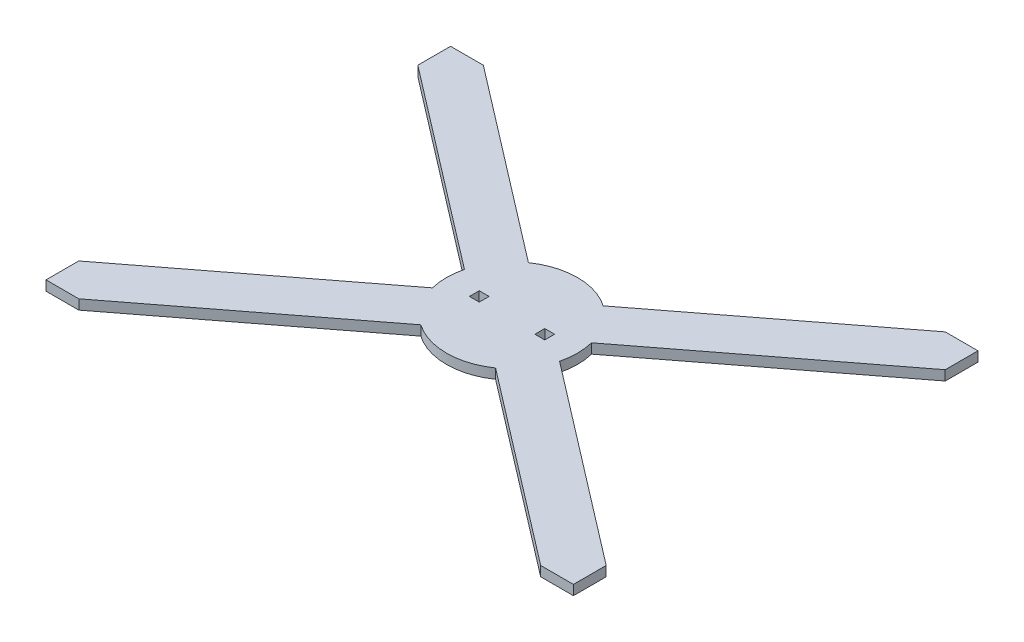
SolidWorks part; units mm, degrees
ref_plane "Alzado" through (0, 0, 0) normal (0, 0, 1) x (1, 0, 0)
ref_plane "Planta" through (0, 0, 0) normal (0, 1, 0) x (1, 0, 0)
ref_plane "Vista lateral" through (0, 0, 0) normal (1, 0, 0) x (0, 0, -1)
sketch "Croquis1" plane through (0, 0, 0) normal (0, 1, 0) x (1, 0, 0)
  line L0 (-161, 103.5) -> (-38.7919, 9.7565)
  line L1 (-40, 40) -> (40, 40) construction
  line L2 (-40, 40) -> (-40, -40) construction
  line L3 (-40, -40) -> (40, -40) construction
  line L4 (40, 40) -> (40, -40) construction
  line L5 (-40, 40) -> (40, -40) construction
  line L6 (-40, -40) -> (40, 40) construction
  line L7 (-161, 123.5) -> (161, 123.5) construction
  line L8 (-161, 123.5) -> (-161, -123.5) construction
  line L9 (-161, -123.5) -> (161, -123.5) construction
  line L10 (161, 123.5) -> (161, -123.5) construction
  line L11 (-161, 123.5) -> (161, -123.5) construction
  line L12 (-161, -123.5) -> (161, 123.5) construction
  line L13 (-161, 103.5) -> (-161, 123.5)
  line L14 (-161, 123.5) -> (-141, 123.5)
  line L15 (-141, 123.5) -> (-22.8238, 32.8493)
  line L16 (-38.7919, -9.7565) -> (-161, -103.5)
  line L17 (-161, -103.5) -> (-161, -123.5)
  line L18 (-161, -123.5) -> (-141, -123.5)
  line L19 (-141, -123.5) -> (-22.8238, -32.8493)
  line L20 (-38.7919, 9.7565) -> (-38.7919, -9.7565) construction
  line L21 (-22.8238, 32.8493) -> (-22.8238, -32.8493) construction
  line L22 (0, 40) -> (0, -40) construction
  line L23 (161, 123.5) -> (141, 123.5)
  line L24 (141, 123.5) -> (22.8238, 32.8493)
  line L25 (161, 103.5) -> (161, 123.5)
  line L26 (161, 103.5) -> (38.7919, 9.7565)
  line L27 (161, -123.5) -> (141, -123.5)
  line L28 (161, -103.5) -> (161, -123.5)
  line L29 (38.7919, -9.7565) -> (161, -103.5)
  line L30 (141, -123.5) -> (22.8238, -32.8493)
  circle A0 centre (0, 0) radius 40 construction
  arc A1 (-38.7919, 9.7565) -> (-38.7919, -9.7565) centre (0, 0) ccw
  arc A2 (-22.8238, 32.8493) -> (22.8238, 32.8493) centre (0, 0) cw
  arc A3 (22.8238, -32.8493) -> (-22.8238, -32.8493) centre (0, 0) cw
  arc A4 (38.7919, 9.7565) -> (38.7919, -9.7565) centre (0, 0) cw
  point P0 (0, 0)
  point P6 (0, 0)
  dimension "D1" = 80
  dimension "D2" = 80
  dimension "D3" = 322
  dimension "D4" = 247
  dimension "D5" = 20
extrude "Saliente-Extruir1" add sketch "Croquis1" along normal blind 6
sketch "Croquis7" plane through (0, 0, 0) normal (0, -1, 0) x (-1, 0, 0)
  circle A0 centre (0, 0) radius 40
  arc A1 (-38.7919, 9.7565) -> (-38.7919, -9.7565) centre (0, 0) ccw construction
extrude "Saliente-Extruir5" add sketch "Croquis7" along normal blind 6
sketch "Croquis5" plane through (0, -6, 0) normal (0, -1, 0) x (1, 0, 0)
  line L0 (13.25, 11) -> (-13.25, 11) construction
  line L1 (-10.25, 8) -> (10.25, 8) construction
  line L2 (-10.25, 8) -> (-10.25, -8) construction
  line L3 (-10.25, -8) -> (10.25, -8) construction
  line L4 (10.25, 8) -> (10.25, -8) construction
  line L5 (-10.25, 8) -> (10.25, -8) construction
  line L6 (-10.25, -8) -> (10.25, 8) construction
  line L7 (-13.25, 11) -> (-13.25, -11) construction
  line L8 (-13.25, -11) -> (13.25, -11) construction
  line L9 (13.25, -11) -> (13.25, -21) construction
  line L10 (13.25, -21) -> (-28.25, -21) construction
  line L11 (-28.25, -21) -> (-28.25, 21) construction
  line L12 (-28.25, 21) -> (13.25, 21) construction
  line L13 (13.25, 21) -> (13.25, 11) construction
  line L14 (0, 11) -> (0, 0) construction
  line L15 (0, 0) -> (0, -11) construction
  line L16 (13.25, 11) -> (28.25, 11) construction
  line L17 (-28.25, 21) -> (28.25, 21) construction
  line L18 (-28.25, 21) -> (-28.25, -21) construction
  line L19 (-28.25, -21) -> (28.25, -21) construction
  line L20 (28.25, 21) -> (28.25, -21) construction
  line L21 (-28.25, 21) -> (28.25, -21) construction
  line L22 (-28.25, -21) -> (28.25, 21) construction
  line L23 (28.25, 11) -> (28.25, 21) construction
  line L24 (28.25, 21) -> (13.25, 21) construction
  line L25 (13.25, -21) -> (28.25, -21) construction
  line L26 (28.25, -21) -> (28.25, -11) construction
  line L27 (28.25, -11) -> (13.25, -11) construction
  line L28 (-9, 7) -> (9, 7) construction
  line L29 (0, 7) -> (0, 0) construction
  line L30 (-9, 7) -> (9, 7) construction
  line L31 (-9, 7.5) -> (9, 7.5) construction
  line L32 (-9, 6.5) -> (9, 6.5) construction
  line L33 (-18.8961, 21) -> (18.8961, 21) construction
  line L34 (18.8961, -21) -> (-18.8961, -21)
  line L35 (-18.8961, 21) -> (-13.25, 21)
  line L36 (-13.25, 21) -> (-13.25, -11)
  line L37 (-13.25, -11) -> (13.25, -11)
  line L38 (13.25, -11) -> (13.25, 21)
  line L39 (13.25, 21) -> (18.8961, 21)
  line L40 (-8, -5.75) -> (8, -5.75) construction
  arc A0 (-9, 7.5) -> (-9, 6.5) centre (-9, 7) ccw construction
  arc A1 (9, 6.5) -> (9, 7.5) centre (9, 7) ccw construction
  arc A2 (-18.8961, 21) -> (-18.8961, -21) centre (0, 0) ccw
  arc A3 (18.8961, 21) -> (18.8961, -21) centre (0, 0) cw
  circle A4 centre (-8, -5.75) radius 1.75 construction
  circle A5 centre (8, -5.75) radius 1.75 construction
  point P0 (0, 0)
  point P26 (0, 7)
  dimension "D11" = 0.5
  dimension "D12" = 3.5
  dimension "D14" = 2.25
  dimension "D1" = 16
  dimension "D2" = 20.5
  dimension "D3" = 3
  dimension "D4" = 3
  dimension "D5" = 10
  dimension "D6" = 10
  dimension "D7" = 15
  dimension "D8" = 3
  dimension "D9" = 18
  dimension "D10" = 1
  dimension "D13" = 2.25
  dimension "D15" = 2.25
extrude "Saliente-Extruir3" add sketch "Croquis5" along normal blind 6
sketch "Croquis6" plane through (0, -12, 0) normal (0, -1, 0) x (1, 0, 0)
  line L0 (18.8961, 21) -> (13.25, 21) construction
  line L1 (-28.25, 21) -> (28.25, 21) construction
  line L2 (-28.25, 21) -> (-28.25, -21) construction
  line L3 (-28.25, -21) -> (28.25, -21) construction
  line L4 (28.25, 21) -> (28.25, -21) construction
  line L5 (-28.25, 21) -> (28.25, -21) construction
  line L6 (-28.25, -21) -> (28.25, 21) construction
  line L7 (-18.8961, 21) -> (-13.25, 21)
  line L8 (-9, 7) -> (9, 7) construction
  line L9 (-9, 7.5) -> (9, 7.5) construction
  line L10 (-9, 6.5) -> (9, 6.5) construction
  line L11 (-18.8961, 21) -> (18.8961, 21) construction
  line L12 (18.8961, -21) -> (-18.8961, -21) construction
  line L18 (13.25, 21) -> (18.8961, 21)
  line L19 (18.8961, -21) -> (-18.8961, -21)
  line L20 (-13.25, 21) -> (-13.25, 3.5)
  line L21 (-13.25, 21) -> (-13.25, -11) construction
  line L22 (-12.75, 3) -> (12.75, 3)
  line L23 (13.25, -11) -> (13.25, 21) construction
  line L24 (13.25, 3.5) -> (13.25, 21)
  line L25 (-13.25, 3.5) -> (13.25, 3.5) construction
  arc A0 (-9, 7.5) -> (-9, 6.5) centre (-9, 7) ccw construction
  arc A1 (9, 6.5) -> (9, 7.5) centre (9, 7) ccw construction
  arc A2 (9, 6.5) -> (9, 7.5) centre (9, 7) ccw construction
  circle A3 centre (0, 0) radius 28.25 construction
  arc A4 (18.8961, 21) -> (18.8961, -21) centre (0, 0) cw construction
  arc A5 (-18.8961, -21) -> (-18.8961, 21) centre (0, 0) cw construction
  arc A6 (-18.8961, 21) -> (-18.8961, -21) centre (0, 0) ccw construction
  arc A7 (-18.8961, -21) -> (-18.8961, 21) centre (0, 0) cw
  arc A8 (18.8961, -21) -> (18.8961, 21) centre (0, 0) ccw
  circle A9 centre (-8, -5.75) radius 1.75
  circle A10 centre (8, -5.75) radius 1.75
  circle A11 centre (-8, -5.75) radius 1.75 construction
  circle A12 centre (8, -5.75) radius 1.75 construction
  arc A13 (-13.25, 3.5) -> (-12.75, 3) centre (-12.75, 3.5) ccw
  arc A14 (12.75, 3) -> (13.25, 3.5) centre (12.75, 3.5) ccw
  point P0 (0, 0)
  point P14 (0, 7)
  dimension "D2" = 0.5
  dimension "D1" = 18
extrude "Saliente-Extruir4" add sketch "Croquis6" along normal blind 6
sketch "Croquis8" plane through (0, -18, 0) normal (0, -1, 0) x (1, 0, 0)
  line L0 (-20, 0) -> (0, 0) construction
  line L1 (-23, 3) -> (-17, 3)
  line L2 (-23, 3) -> (-23, -3)
  line L3 (-23, -3) -> (-17, -3)
  line L4 (-17, 3) -> (-17, -3)
  line L5 (-23, 3) -> (-17, -3) construction
  line L6 (-23, -3) -> (-17, 3) construction
  line L7 (0, 0) -> (0, -21) construction
  line L8 (-18.8961, -21) -> (18.8961, -21) construction
  line L9 (23, -3) -> (17, -3)
  line L10 (23, 3) -> (23, -3)
  line L11 (23, 3) -> (17, 3)
  line L12 (17, 3) -> (17, -3)
  point P0 (-20, 0)
  dimension "D1" = 6
  dimension "D2" = 6
  dimension "D3" = 20
extrude "Cortar-Extruir1" cut sketch "Croquis8" against normal through all
sketch "Croquis9" plane through (0, -18, 0) normal (0, -1, 0) x (-1, 0, 0)
  circle A0 centre (0, 0) radius 40
  circle A1 centre (0, 0) radius 40 construction
extrude "Cortar-Extruir2" cut sketch "Croquis9" against normal up to surface (18 mm away) up to face at (-105.3417, 0, 78.9106)
